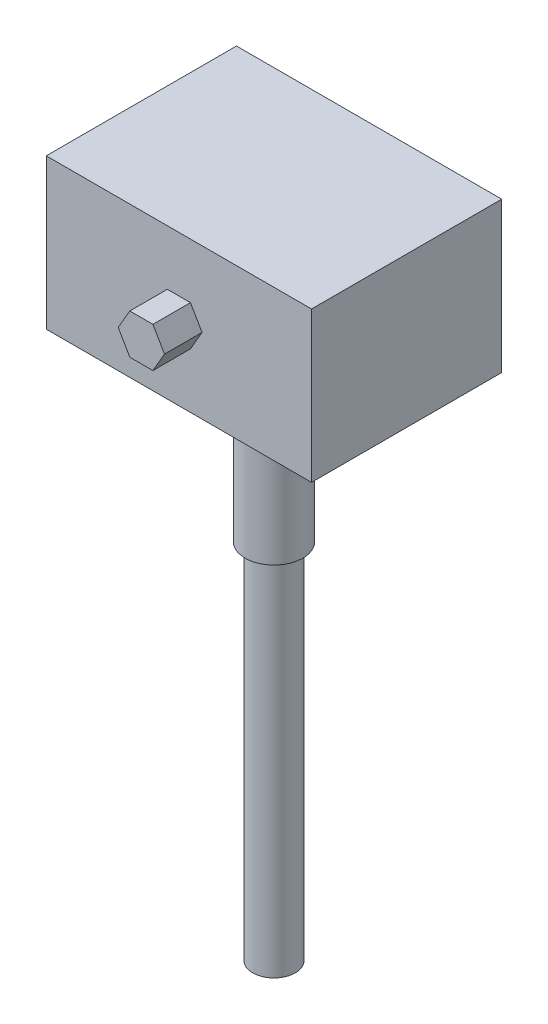
SolidWorks part; units mm, degrees
ref_plane "Front Plane" through (0, 0, 0) normal (0, 0, 1) x (1, 0, 0)
ref_plane "Top Plane" through (0, 0, 0) normal (0, 1, 0) x (1, 0, 0)
ref_plane "Right Plane" through (0, 0, 0) normal (1, 0, 0) x (0, 0, -1)
sketch "Sketch1" plane through (0, 0, 0) normal (0, 1, 0) x (1, 0, 0)
  line L1 (-53, 38) -> (53, 38)
  line L2 (-53, 38) -> (-53, -38)
  line L3 (-53, -38) -> (53, -38)
  line L4 (53, 38) -> (53, -38)
  line L5 (-53, 38) -> (53, -38) construction
  line L6 (-53, -38) -> (53, 38) construction
  point P0 (0, 0)
  dimension "D1" = 76
  dimension "D2" = 106
extrude "Boss-Extrude1" add sketch "Sketch1" along normal blind 60
sketch "Sketch2" plane through (0, 0, 38) normal (0, 0, 1) x (1, 0, 0)
  line L1 (9.2376, 30) -> (4.6188, 38)
  line L2 (4.6188, 38) -> (-4.6188, 38)
  line L3 (-4.6188, 38) -> (-9.2376, 30)
  line L4 (-9.2376, 30) -> (-4.6188, 22)
  line L5 (-4.6188, 22) -> (4.6188, 22)
  line L6 (4.6188, 22) -> (9.2376, 30)
  circle A0 centre (0, 30) radius 8 construction
  dimension "D1" = 16
  dimension "D2" = 30
  dimension "D3" = 0
extrude "Boss-Extrude2" add sketch "Sketch2" along normal blind 15
sketch "Sketch3" plane through (0, 0, 0) normal (0, -1, 0) x (1, 0, 0)
  circle A0 centre (0, 0) radius 14
  dimension "D1" = 28
extrude "Boss-Extrude3" add sketch "Sketch3" along normal blind 15
sketch "Sketch4" plane through (0, -15, 0) normal (0, -1, 0) x (1, 0, 0)
  circle A0 centre (0, 0) radius 5
  dimension "D1" = 10
extrude "Boss-Extrude4" add sketch "Sketch4" along normal blind 11
sketch "Sketch5" plane through (0, -26, 0) normal (0, -1, 0) x (1, 0, 0)
  circle A0 centre (0, 0) radius 11.5
  dimension "D1" = 23
extrude "Boss-Extrude5" add sketch "Sketch5" along normal blind 40
sketch "Sketch6" plane through (0, -66, 0) normal (0, -1, 0) x (1, 0, 0)
  circle A0 centre (0, 0) radius 8.5
  dimension "D1" = 17
extrude "Boss-Extrude6" add sketch "Sketch6" along normal blind 145
